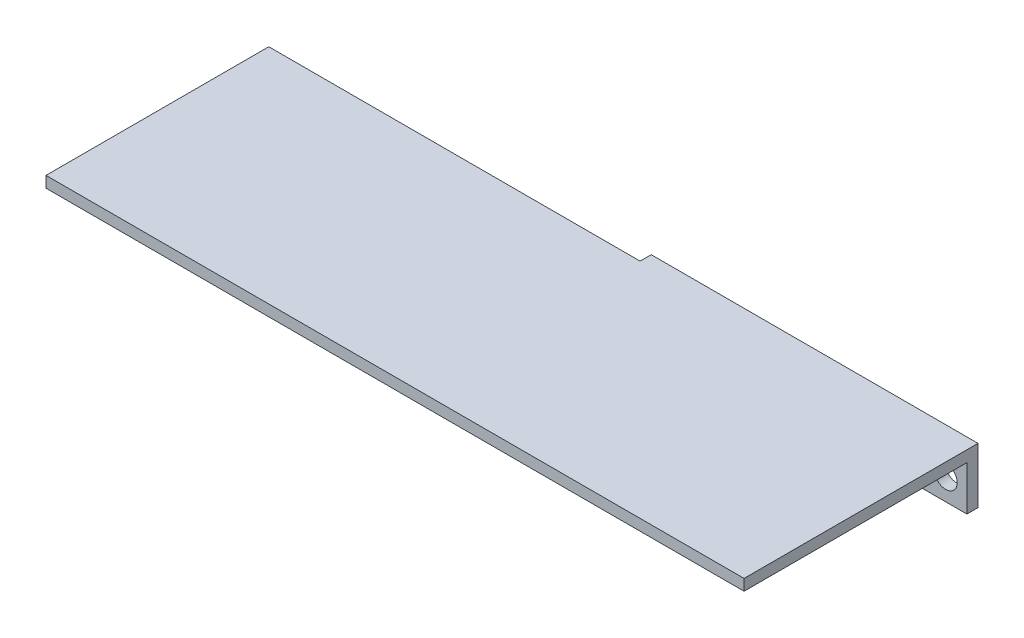
SolidWorks part; units mm, degrees
material "PTFE(普通)"
ref_plane "前视基准面" through (0, 0, 0) normal (0, 0, 1) x (1, 0, 0)
ref_plane "上视基准面" through (0, 0, 0) normal (0, 1, 0) x (1, 0, 0)
ref_plane "右视基准面" through (0, 0, 0) normal (1, 0, 0) x (0, 0, -1)
other "Configuration Table"
sketch "草图1" plane through (0, 0, 0) normal (0, 0, 1) x (1, 0, 0)
  line L1 (22, -3) -> (-22, -3)
  line L2 (22, -3) -> (22, 3)
  line L3 (22, 3) -> (-22, 3)
  line L4 (-22, -3) -> (-22, 3)
  line L5 (22, -3) -> (-22, 3) construction
  line L6 (22, 3) -> (-22, -3) construction
  circle A0 centre (-19.1442, 0) radius 1.55
  circle A1 centre (19.1442, 0) radius 1.55
  point P0 (0, 0)
  point P6 (-19.1442, 0)
  point P7 (19.1442, 0)
  dimension "D3" = 3.1
  dimension "D4" = 3.1
  dimension "D1" = 19.1442
  dimension "D2" = 19.1442
  dimension "D5" = 22
  dimension "D6" = 3
extrude "凸台-拉伸1" add sketch "草图1" along normal blind 1.5
sketch "草图2" plane through (0, 3, 0) normal (0, 1, 0) x (1, 0, 0)
  line L1 (-22, 0) -> (22, 0)
  line L2 (-22, 0) -> (-22, -1.5)
  line L3 (-22, -1.5) -> (22, -1.5)
  line L4 (22, 0) -> (22, -1.5)
extrude "凸台-拉伸2" add sketch "草图2" along normal blind 1.5
sketch "草图3" plane through (0, 0, 1.5) normal (0, 0, 1) x (1, 0, 0)
  line L0 (22, -3) -> (22, 4.5) construction
  line L1 (-22, 4.5) -> (22, 4.5)
  line L2 (-22, 4.5) -> (-22, 3)
  line L3 (-22, 3) -> (22, 3)
  line L4 (22, 4.5) -> (22, 3)
  dimension "D1" = 1.5
sketch "草图4" plane through (0, 0, 0) normal (0, 0, -1) x (-1, 0, 0)
  line L1 (-22, 4.5) -> (22, 4.5)
  line L2 (-22, 4.5) -> (-22, 3)
  line L3 (-22, 3) -> (22, 3)
  line L4 (22, 4.5) -> (22, 3)
extrude "凸台-拉伸4" add sketch "草图4" against normal blind 31.5 contours L1 L4 L3 L2
sketch "草图6" plane through (-22, 0, 0) normal (-1, 0, 0) x (0, 0, 1)
  line L0 (1.5, 4.5) -> (1.5, 3) construction
  line L1 (1.5, 4.5) -> (31.5, 4.5)
  line L2 (1.5, 4.5) -> (1.5, 3)
  line L3 (1.5, 3) -> (31.5, 3)
  line L4 (31.5, 4.5) -> (31.5, 3)
  line L5 (0, 4.5) -> (31.5, 4.5) construction
extrude "凸台-拉伸5" add sketch "草图6" along normal blind 50
